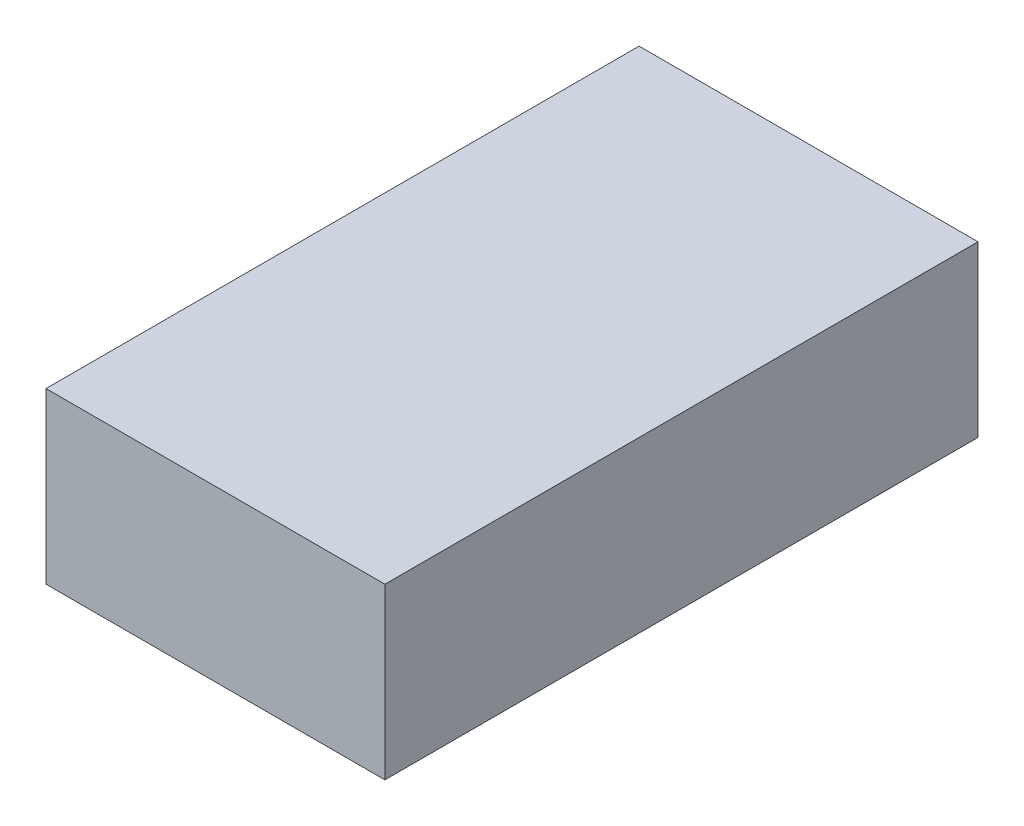
SolidWorks part; units mm, degrees
ref_plane "正面" through (0, 0, 0) normal (0, 0, 1) x (1, 0, 0)
ref_plane "平面" through (0, 0, 0) normal (0, 1, 0) x (1, 0, 0)
ref_plane "右側面" through (0, 0, 0) normal (1, 0, 0) x (0, 0, -1)
sketch "ｽｹｯﾁ1" plane through (0, 0, 0) normal (0, 0, 1) x (1, 0, 0)
  line L1 (0, 0) -> (160, 0)
  line L2 (0, 0) -> (0, 80)
  line L3 (0, 80) -> (160, 80)
  line L4 (160, 0) -> (160, 80)
  dimension "D1" = 80
  dimension "D2" = 160
extrude "ﾎﾞｽ - 押し出し1" add sketch "ｽｹｯﾁ1" along normal blind 280
